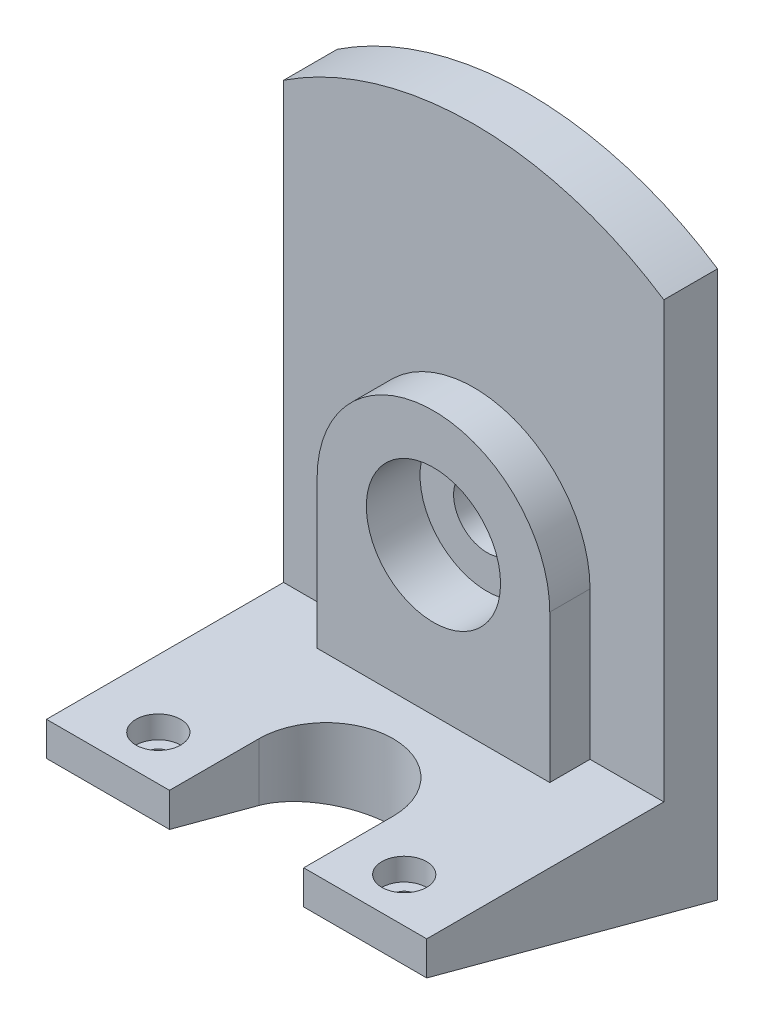
SolidWorks part; units mm, degrees
material "ABS"
ref_plane "Front Plane" through (0, 0, 0) normal (1, 0, 0) x (0, 1, 0)
ref_plane "Top Plane" through (0, 0, 0) normal (0, 0, 1) x (0, 1, 0)
ref_plane "Right Plane" through (0, 0, 0) normal (0, 1, 0) x (-1, 0, 0)
sketch "Sketch1" plane through (0, 0, 0) normal (1, 0, 0) x (0, 1, 0)
  line L0 (0, 0) -> (17.4167, 65)
  line L1 (17.4167, 65) -> (25, 65)
  line L2 (25, 65) -> (25, 12)
  line L3 (25, 12) -> (135, 12)
  line L4 (135, 12) -> (135, 0)
  line L5 (135, 0) -> (0, 0)
  dimension "D1" = 135
  dimension "D2" = 12
  dimension "D3" = 15
  dimension "D4" = 25
  dimension "D5" = 65
extrude "Boss-Extrude1" add sketch "Sketch1" along normal mid plane 85
sketch "Sketch3" plane through (0, 0, 12) normal (0, 0, 1) x (1, 0, 0)
  line L0 (-42.5, 135) -> (-42.5, 25) construction
  line L1 (42.5, 135) -> (42.5, 25) construction
  line L2 (42.5, 135) -> (-42.5, 135) construction
  arc A0 (-42.5, 122.2086) -> (42.5, 122.2086) centre (0, 58) cw
  dimension "D1" = 77
extrude "Cut-Extrude1" cut sketch "Sketch3" against normal through all both and the other way through all
sketch "Sketch4" plane through (0, 0, 12) normal (0, 0, 1) x (1, 0, 0)
  line L0 (-26, 25) -> (-26, 58)
  line L1 (42.5, 25) -> (-42.5, 25) construction
  line L2 (26, 58) -> (26, 25)
  line L3 (42.5, 25) -> (-42.5, 25) construction
  line L4 (26, 25) -> (-26, 25)
  arc A0 (-26, 58) -> (26, 58) centre (0, 58) cw
  arc A1 (42.5, 122.2086) -> (-42.5, 122.2086) centre (0, 58) ccw construction
  dimension "D1" = 26
extrude "Boss-Extrude2" add sketch "Sketch4" along normal blind 9
hole_wizard "CBORE for M10 Hex Head Bolt1" positions "3DSketch2" profile "Sketch7" counterbore size "M10" standard "ANSI Metric" end condition through all
sketch3d "3DSketch2"
  line L0 (0, 58, 21) -> (0, 58, 12) construction
  point P0 (0, 58, 21)
sketch "Sketch7" plane through (0, 58, 21) normal (1, 0, 0) x (0, -1, 0)
  line L0 (0, 0) -> (0, 21)
  line L1 (0, 21) -> (7.5, 21)
  line L3 (7.5, 21) -> (7.5, 12)
  line L4 (7.5, 12) -> (15, 12)
  line L5 (15, 12) -> (15, 0)
  line L7 (15, 0) -> (0, 0)
  line L11 (0, -6.35) -> (0, 107.95) construction
  dimension "Thru Hole Dia." = 15
  dimension "Thru Hole Depth" = 21
  dimension "C'Bore Dia." = 30
  dimension "C'Bore Depth" = 12
sketch "Sketch8" plane through (0, 25, 0) normal (0, 1, 0) x (-1, 0, 0)
  line L0 (-15, 65) -> (-15, 45)
  line L1 (-42.5, 65) -> (42.5, 65) construction
  line L2 (15, 45) -> (15, 65)
  line L3 (15, 65) -> (-15, 65)
  arc A0 (-15, 45) -> (15, 45) centre (0, 45) ccw
  dimension "D1" = 15
  dimension "D2" = 20
  dimension "D3" = 15
extrude "Cut-Extrude2" cut sketch "Sketch8" against normal through all both and the other way through all
sketch "Sketch9" plane through (0, 25, 0) normal (0, 1, 0) x (-1, 0, 0)
  line L0 (-42.5, 65) -> (-15, 65) construction
  line L1 (-27.5, 65) -> (27.5, 65)
  line L2 (-27.5, 65) -> (-27.5, 55)
  line L3 (-27.5, 55) -> (27.5, 55)
  line L4 (27.5, 65) -> (27.5, 55)
  line L5 (-27.5, 65) -> (27.5, 55) construction
  line L6 (-27.5, 55) -> (27.5, 65) construction
  point P0 (0, 60)
  point P1 (27.5, 55)
  point P8 (0.085, 59.817)
  point P10 (-27.5294, 55.0588)
  dimension "D1" = 27.5
  dimension "D2" = 55
  dimension "D3" = 10
hole_wizard "CBORE for M10 Hex Head Bolt2" positions "Sketch9" profile "Sketch10" counterbore size "M10" standard "ANSI Metric" end condition through all
sketch "Sketch10" plane through (0, 25, 60) normal (1, 0, 0) x (0, 0, 1)
  line L0 (0, 0) -> (0, 25)
  line L1 (0, 25) -> (2.5, 25)
  line L3 (2.5, 25) -> (2.5, 5)
  line L4 (2.5, 5) -> (5, 5)
  line L5 (5, 5) -> (5, 0)
  line L7 (5, 0) -> (0, 0)
  line L11 (0, -6.35) -> (0, 107.95) construction
  dimension "Thru Hole Dia." = 5
  dimension "Thru Hole Depth" = 25
  dimension "C'Bore Dia." = 10
  dimension "C'Bore Depth" = 5
